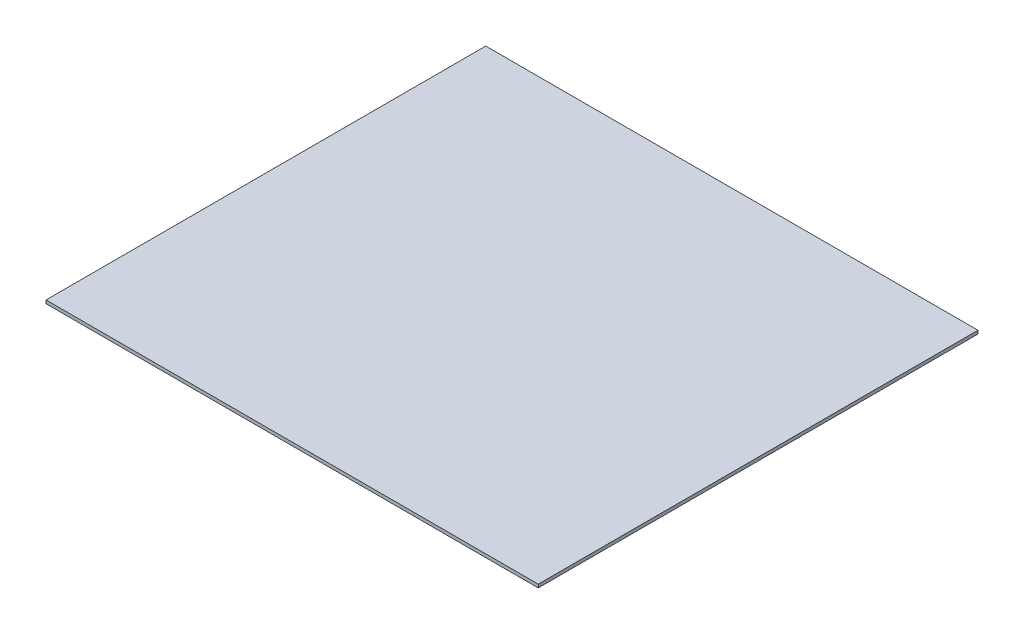
SolidWorks part; units mm, degrees
material "Acrylic (Medium-high impact)"
ref_plane "Front Plane" through (0, 0, 0) normal (0, 0, 1) x (1, 0, 0)
ref_plane "Top Plane" through (0, 0, 0) normal (0, 1, 0) x (1, 0, 0)
ref_plane "Right Plane" through (0, 0, 0) normal (1, 0, 0) x (0, 0, -1)
sketch "Sketch1" plane through (0, 0, 0) normal (0, 1, 0) x (1, 0, 0)
  line L1 (0, 0) -> (-750, 0)
  line L2 (0, 0) -> (0, 670)
  line L3 (0, 670) -> (-750, 670)
  line L4 (-750, 0) -> (-750, 670)
  line L5 (0, 0) -> (-750, 670) construction
  line L6 (0, 670) -> (-750, 0) construction
  point P4 (-375, 335)
  dimension "D1" = 750
  dimension "D2" = 670
extrude "Boss-Extrude1" add sketch "Sketch1" along normal blind 5
